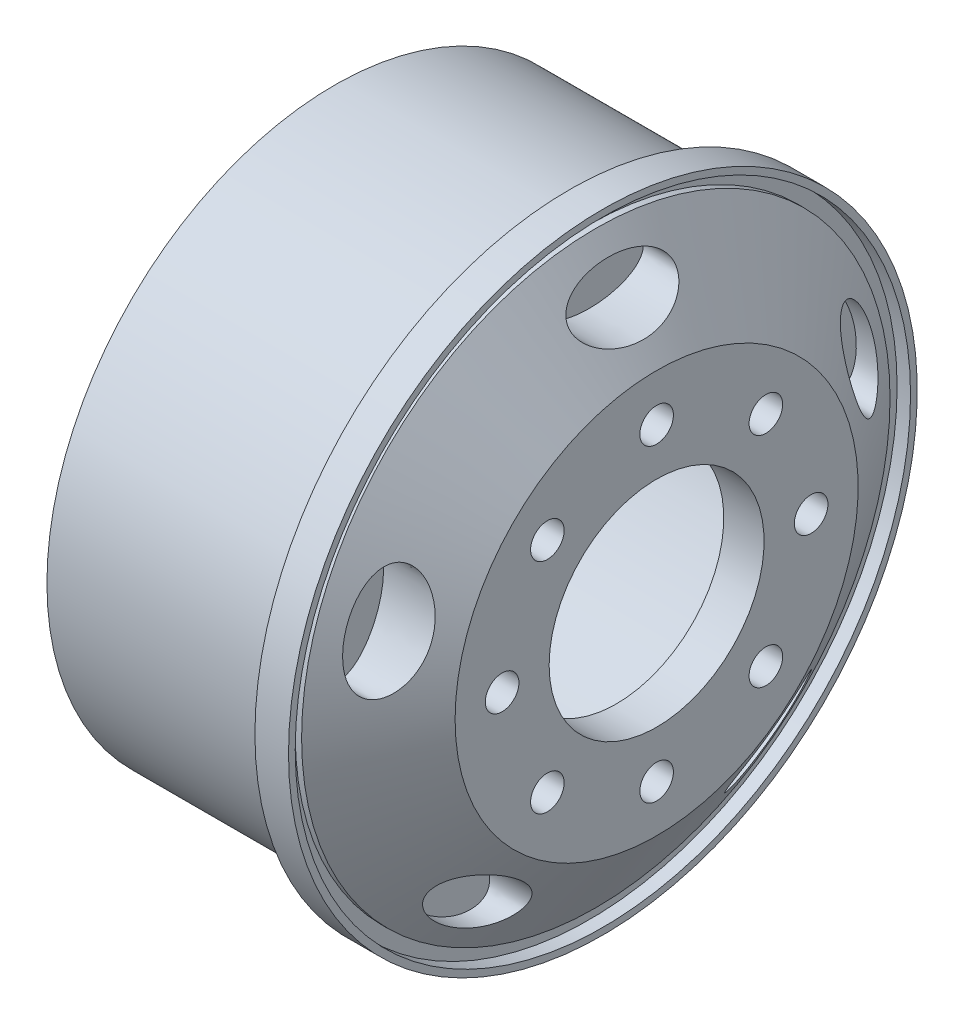
SolidWorks part; units mm, degrees
ref_plane "Front Plane" through (0, 0, 0) normal (0, 0, 1) x (1, 0, 0)
ref_plane "Top Plane" through (0, 0, 0) normal (0, 1, 0) x (1, 0, 0)
ref_plane "Right Plane" through (0, 0, 0) normal (1, 0, 0) x (0, 0, -1)
sketch "Sketch3" plane through (0, 0, 0) normal (0, 1, 0) x (1, 0, 0)
  line L0 (-29.7742, 0) -> (36.8095, 0) construction
  line L2 (10.3693, 23.4) -> (8.8693, 23.4)
  line L7 (8.8693, 23.4) -> (8.8693, 21.4)
  line L8 (8.8693, 21.4) -> (-8.6107, 21.4)
  line L9 (-8.6107, 21.4) -> (-8.6107, 18.2319)
  line L10 (10.3693, 23.4) -> (11.3693, 23.4)
  line L11 (11.3693, 23.4) -> (11.3693, 22.9)
  line L12 (11.3693, 22.9) -> (10.3693, 22.9)
  line L13 (10.8435, 21.9) -> (15.3693, 15)
  line L14 (15.3693, 15) -> (15.3693, 8)
  line L16 (-8.6107, 18.2319) -> (9.2115, 18.2319)
  line L17 (9.2115, 18.2319) -> (12.3693, 13.4176)
  line L18 (12.3693, 13.4176) -> (12.3693, 8)
  line L21 (10.3693, 22.9) -> (10.3693, 21.9)
  line L22 (10.3693, 21.9) -> (10.8435, 21.9)
  line L23 (12.3693, 8) -> (15.3693, 8)
  point P3 (13.8693, 8)
  dimension "D1" = 1.5
  dimension "D2" = 46.8
  dimension "D3" = 2
  dimension "D4" = 42.8
  dimension "D5" = 18.98
  dimension "D6" = 1
  dimension "D7" = 0.5
  dimension "D8" = 30
  dimension "D9" = 5
  dimension "D10" = 3
  dimension "D11" = 1
  dimension "D12" = 20.98
  dimension "D13" = 13.4176
  dimension "D14" = 123.261
  dimension "D15" = 18.2319
  dimension "D16" = 16
revolve "Revolve1" add sketch "Sketch3" angle 360 about L0
sketch "Sketch4" plane through (15.3693, 0, 0) normal (1, 0, 0) x (0, 0, -1)
  circle A0 centre (0, 0) radius 11.5 construction
  circle A1 centre (0, 11.5) radius 1.25
  circle A2 centre (8.1317, 8.1317) radius 1.25
  circle A3 centre (11.5, 0) radius 1.25
  circle A4 centre (8.1317, -8.1317) radius 1.25
  circle A5 centre (0, -11.5) radius 1.25
  circle A6 centre (-8.1317, -8.1317) radius 1.25
  circle A7 centre (-11.5, 0) radius 1.25
  circle A8 centre (0, 0) radius 18.5 construction
  circle A9 centre (-8.1317, 8.1317) radius 1.25
  ellipse E0 centre (0, 18.5) end of major axis (4, 18.5) minor radius 2
  ellipse E1 centre (17.5945, 5.7168) end of major axis (18.8306, 1.9126) minor radius 2
  ellipse E2 centre (10.874, -14.9668) end of major axis (7.638, -17.318) minor radius 2
  ellipse E3 centre (-10.874, -14.9668) end of major axis (-14.1101, -12.6157) minor radius 2
  ellipse E4 centre (-17.5945, 5.7168) end of major axis (-16.3585, 9.521) minor radius 2
  point P20 (0, 0)
  point P52 (0, 0)
  dimension "D1" = 23
  dimension "D2" = 2.5
  dimension "D4" = 37
  dimension "D5" = 8
  dimension "D6" = 4
  dimension "D3" = 8
  dimension "D7" = 5
extrude "Cut-Extrude1" cut sketch "Sketch4" against normal blind 5
